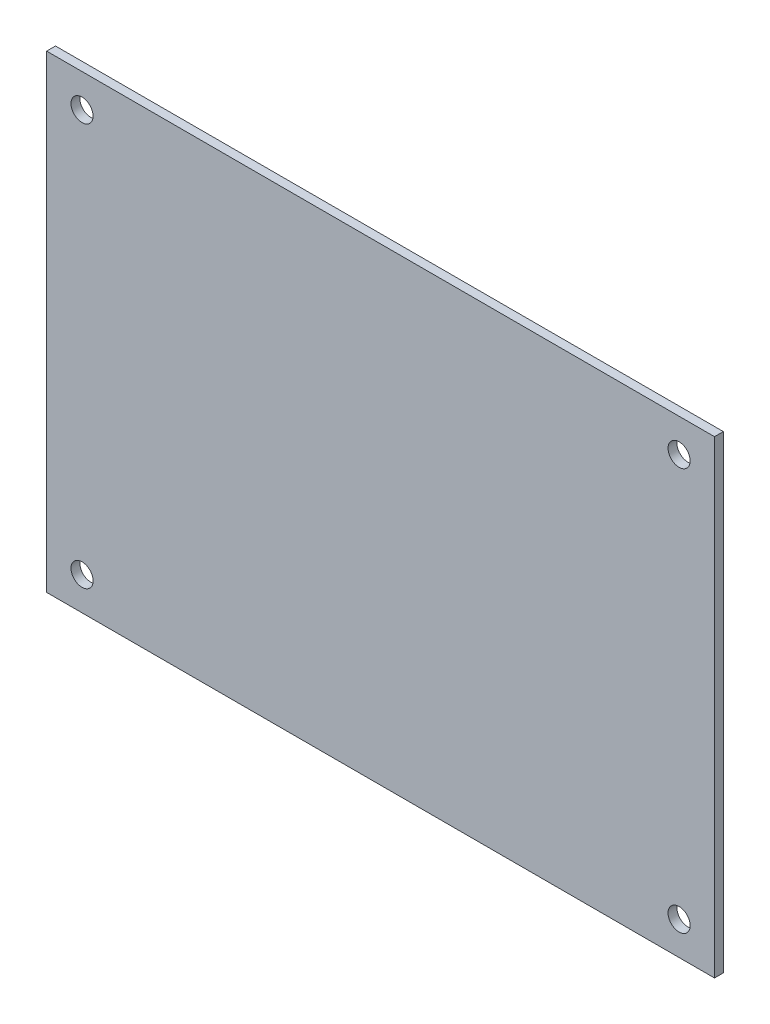
SolidWorks part; units mm, degrees
ref_plane "Front Plane" through (0, 0, 0) normal (0, 0, 1) x (1, 0, 0)
ref_plane "Top Plane" through (0, 0, 0) normal (0, 1, 0) x (1, 0, 0)
ref_plane "Right Plane" through (0, 0, 0) normal (1, 0, 0) x (0, 0, -1)
sketch "Sketch1" plane through (0, 0, 0) normal (0, 0, 1) x (1, 0, 0)
  line L1 (0, 0) -> (155, 0)
  line L2 (0, 0) -> (0, 110)
  line L3 (0, 110) -> (155, 110)
  line L4 (155, 0) -> (155, 110)
  dimension "D1" = 155
  dimension "D2" = 110
extrude "Boss-Extrude1" add sketch "Sketch1" along normal blind 80 contours L2 L1 L4 L3
sketch "Sketch2" plane through (0, 0, 80) normal (0, 0, 1) x (1, 0, 0)
  line L0 (0, 110) -> (2, 110) construction
  line L1 (0, 110) -> (155, 110) construction
  line L2 (0, 110) -> (0, 108) construction
  line L3 (0, 0) -> (0, 110) construction
  line L4 (155, 0) -> (155, 2) construction
  line L5 (155, 0) -> (155, 110) construction
  line L6 (155, 0) -> (153, 0) construction
  line L7 (0, 0) -> (155, 0) construction
  line L8 (0, 108) -> (2, 108) construction
  line L9 (2, 108) -> (2, 110) construction
  line L10 (155, 2) -> (153, 2) construction
  line L11 (153, 2) -> (153, 0) construction
  line L13 (153, 2) -> (2, 2)
  line L14 (153, 2) -> (153, 108)
  line L15 (153, 108) -> (2, 108)
  line L16 (2, 2) -> (2, 108)
  dimension "D1" = 2
  dimension "D2" = 2
  dimension "D3" = 2
  dimension "D4" = 2
extrude "Cut-Extrude1" cut sketch "Sketch2" against normal blind 78 contours L14 L13 L16 L15
sketch "Sketch3" plane through (0, 0, 2) normal (0, 0, 1) x (1, 0, 0)
  line L0 (2, 2) -> (6, 2) construction
  line L1 (153, 2) -> (2, 2) construction
  line L2 (153, 2) -> (149, 2) construction
  line L3 (2, 108) -> (6, 108) construction
  line L4 (153, 108) -> (2, 108) construction
  line L5 (2, 108) -> (2, 104.5) construction
  line L6 (2, 2) -> (2, 108) construction
  line L7 (149, 2) -> (149, 5.5) construction
  line L8 (2, 104.5) -> (6, 104.5) construction
  line L9 (6, 104.5) -> (6, 108) construction
  line L10 (6, 5.5) -> (10, 5.5) construction
  line L11 (6, 104.5) -> (149, 104.5)
  line L12 (6, 104.5) -> (6, 5.5)
  line L13 (6, 5.5) -> (149, 5.5)
  line L14 (149, 104.5) -> (149, 5.5)
  line L15 (10, 5.5) -> (10, 9.5) construction
  line L16 (149, 104.5) -> (145, 104.5) construction
  line L17 (145, 104.5) -> (145, 100.5) construction
  line L19 (10, 9.5) -> (145, 9.5)
  line L20 (10, 9.5) -> (10, 100.5)
  line L21 (10, 100.5) -> (145, 100.5)
  line L22 (145, 9.5) -> (145, 100.5)
  circle A0 centre (145, 100.5) radius 2.5
  circle A1 centre (145, 9.5) radius 2.5
  circle A2 centre (10, 9.5) radius 2.5
  circle A3 centre (10, 100.5) radius 2.5
  dimension "D10" = 5
  dimension "D11" = 5
  dimension "D12" = 5
  dimension "D13" = 5
  dimension "D1" = 4
  dimension "D2" = 3.5
  dimension "D3" = 4
  dimension "D4" = 4
  dimension "D5" = 3.5
  dimension "D6" = 4
  dimension "D7" = 4
  dimension "D8" = 4
  dimension "D9" = 4
extrude "Cut-Extrude2" cut sketch "Sketch3" against normal blind 2 contours A3 | A0 | A2 | A1
sketch "Sketch4" plane through (155, 0, 0) normal (1, 0, 0) x (0, 0, -1)
  line L1 (-53.75, 59.1) -> (-26.25, 59.1)
  line L3 (0, 55) -> (-80, 55) construction
  line L4 (0, 0) -> (0, 110) construction
  line L5 (-80, 0) -> (-80, 110) construction
  line L7 (-26.25, 105.9) -> (-26.25, 59.1)
  line L14 (-53.75, 105.9) -> (-26.25, 105.9)
  line L15 (-53.75, 105.9) -> (-53.75, 59.1)
  dimension "D1" = 46.8
  dimension "D2" = 27.5
sketch "Sketch7" plane through (0, 110, 0) normal (0, 1, 0) x (1, 0, 0)
  line L0 (0, -40) -> (155, -40) construction
  line L1 (0, -80) -> (0, 0) construction
  line L2 (155, -80) -> (155, 0) construction
  line L3 (77.5, 0) -> (77.5, -80) construction
  line L4 (0, 0) -> (155, 0) construction
  line L5 (0, -80) -> (155, -80) construction
  line L6 (110.52, -65.4) -> (95.28, -65.4) construction
  line L7 (44.48, -65.4) -> (110.52, -65.4)
  line L8 (44.48, -65.4) -> (44.48, -14.6)
  line L9 (44.48, -14.6) -> (110.52, -14.6)
  line L10 (110.52, -65.4) -> (110.52, -14.6)
  line L11 (44.48, -65.4) -> (110.52, -14.6) construction
  line L12 (44.48, -14.6) -> (110.52, -65.4) construction
  line L13 (95.28, -65.4) -> (95.28, -62.86) construction
  line L14 (110.52, -14.6) -> (95.28, -14.6) construction
  line L15 (44.48, -14.6) -> (44.48, -20.1445) construction
  line L16 (44.48, -65.4) -> (44.48, -47.62) construction
  line L17 (95.28, -14.6) -> (95.28, -17.14) construction
  line L18 (44.48, -65.4) -> (44.48, -19.68) construction
  circle A0 centre (44.48, -20.1445) radius 1.6
  circle A1 centre (95.28, -17.14) radius 1.6
  circle A2 centre (95.28, -62.86) radius 1.6
  circle A3 centre (44.48, -47.62) radius 1.6
  point P12 (77.5, -40)
  dimension "D9" = 3.2
  dimension "D10" = 3.2
  dimension "D11" = 3.2
  dimension "D12" = 3.2
  dimension "D1" = 66.04
  dimension "D2" = 50.8
  dimension "D3" = 15.24
  dimension "D4" = 2.54
  dimension "D5" = 15.24
  dimension "D6" = 2.54
  dimension "D7" = 17.78
  dimension "D8" = 45.72
extrude "Cut-Extrude7" cut sketch "Sketch7" against normal blind 2 contours A0 | A1 | A3 | A2
extrude "Cut-Extrude8" cut sketch "Sketch4" against normal blind 2
sketch "Sketch8" plane through (155, 0, 0) normal (1, 0, 0) x (0, 0, -1)
  line L0 (-80, 55) -> (0, 55) construction
  line L1 (-80, 0) -> (-80, 110) construction
  line L2 (0, 0) -> (0, 110) construction
  line L3 (0, 0) -> (-2, 0) construction
  line L4 (-80, 0) -> (0, 0) construction
  line L5 (-2, 0) -> (-2, 2) construction
  line L6 (-80, 0) -> (-78, 0) construction
  line L7 (-78, 0) -> (-78, 2) construction
  line L8 (-70, 2) -> (-70, 55)
  line L9 (-78, 2) -> (-74, 2)
  line L10 (-78, 2) -> (-78, 55)
  line L11 (-78, 55) -> (-74, 55)
  line L12 (-74, 2) -> (-74, 55)
  line L13 (-70, 2) -> (-66, 2)
  line L14 (-66, 2) -> (-66, 55)
  line L15 (-70, 55) -> (-66, 55)
  line L16 (-62, 2) -> (-62, 55)
  line L17 (-62, 2) -> (-58, 2)
  line L18 (-58, 2) -> (-58, 55)
  line L19 (-62, 55) -> (-58, 55)
  line L20 (-54, 2) -> (-54, 55)
  line L21 (-54, 2) -> (-50, 2)
  line L22 (-50, 2) -> (-50, 55)
  line L23 (-54, 55) -> (-50, 55)
  line L24 (-46, 2) -> (-46, 55)
  line L25 (-46, 2) -> (-42, 2)
  line L26 (-42, 2) -> (-42, 55)
  line L27 (-46, 55) -> (-42, 55)
  line L28 (-38, 2) -> (-38, 55)
  line L29 (-38, 2) -> (-34, 2)
  line L30 (-34, 2) -> (-34, 55)
  line L31 (-38, 55) -> (-34, 55)
  line L32 (-30, 2) -> (-30, 55)
  line L33 (-30, 2) -> (-26, 2)
  line L34 (-26, 2) -> (-26, 55)
  line L35 (-30, 55) -> (-26, 55)
  line L36 (-22, 2) -> (-22, 55)
  line L37 (-22, 2) -> (-18, 2)
  line L38 (-18, 2) -> (-18, 55)
  line L39 (-22, 55) -> (-18, 55)
  line L40 (-14, 2) -> (-14, 55)
  line L41 (-14, 2) -> (-10, 2)
  line L42 (-10, 2) -> (-10, 55)
  line L43 (-14, 55) -> (-10, 55)
  line L44 (-6, 2) -> (-6, 55)
  line L45 (-6, 2) -> (-2, 2)
  line L46 (-2, 2) -> (-2, 55)
  line L47 (-6, 55) -> (-2, 55)
  dimension "D1" = 2
  dimension "D2" = 2
  dimension "D3" = 2
  dimension "D4" = 2
  dimension "D5" = 4
extrude "Cut-Extrude9" cut sketch "Sketch8" against normal blind 2
sketch "Sketch9" plane through (0, 110, 0) normal (0, 1, 0) x (1, 0, 0)
  line L0 (0, -40) -> (155, -40) construction
  line L1 (0, -80) -> (0, 0) construction
  line L2 (155, -80) -> (155, 0) construction
  line L3 (155, -40) -> (120, -40) construction
  line L4 (120, -40) -> (120, -26) construction
  line L5 (120, -26) -> (113, -26) construction
  line L7 (113, -26) -> (127, -26)
  line L8 (113, -26) -> (113, -12)
  line L9 (113, -12) -> (127, -12)
  line L10 (127, -26) -> (127, -12)
  dimension "D1" = 35
  dimension "D2" = 14
  dimension "D3" = 7
  dimension "D4" = 14
  dimension "D5" = 14
extrude "Cut-Extrude10" cut sketch "Sketch9" against normal blind 2
sketch "Sketch10" plane through (0, 0, 0) normal (-1, 0, 0) x (0, 0, 1)
  line L0 (40, 110) -> (40, 0) construction
  line L1 (80, 110) -> (0, 110) construction
  line L2 (80, 0) -> (0, 0) construction
  line L3 (80, 55) -> (0, 55) construction
  line L4 (80, 0) -> (80, 110) construction
  line L5 (0, 0) -> (0, 110) construction
  line L6 (40, 55) -> (80, 55) construction
  line L7 (80, 55) -> (60, 55) construction
  line L8 (60, 55) -> (58, 55) construction
  line L9 (40, 95) -> (42.5, 95) construction
  line L10 (40, 15) -> (76, 15)
  line L11 (40, 15) -> (40, 95)
  line L12 (40, 95) -> (76, 95)
  line L13 (76, 15) -> (76, 95)
  line L14 (40, 15) -> (76, 95) construction
  line L15 (40, 95) -> (76, 15) construction
  line L16 (42.5, 95) -> (42.5, 92.5) construction
  line L17 (76, 15) -> (73.5, 15) construction
  line L18 (73.5, 15) -> (73.5, 17.5) construction
  line L19 (76, 15) -> (76, 19.4) construction
  line L20 (42.5, 92.5) -> (73.5, 92.5)
  line L21 (42.5, 92.5) -> (42.5, 17.5)
  line L22 (42.5, 17.5) -> (73.5, 17.5)
  line L23 (73.5, 92.5) -> (73.5, 17.5)
  line L24 (76, 19.4) -> (70.6, 19.4) construction
  line L25 (40, 95) -> (45.4, 95) construction
  line L26 (45.4, 95) -> (45.4, 90.6) construction
  line L28 (45.4, 90.6) -> (70.6, 90.6)
  line L29 (45.4, 90.6) -> (45.4, 19.4)
  line L30 (45.4, 19.4) -> (70.6, 19.4)
  line L31 (70.6, 90.6) -> (70.6, 19.4)
  circle A0 centre (73.5, 92.5) radius 1.25
  circle A1 centre (73.5, 17.5) radius 1.25
  circle A2 centre (42.5, 17.5) radius 1.25
  circle A3 centre (42.5, 92.5) radius 1.25
  dimension "D8" = 2.5
  dimension "D9" = 2.5
  dimension "D10" = 2.5
  dimension "D11" = 2.5
  dimension "D1" = 2
  dimension "D2" = 80
  dimension "D3" = 36
  dimension "D4" = 2.5
  dimension "D5" = 2.5
  dimension "D6" = 2.5
  dimension "D7" = 2.5
  dimension "D12" = 4.4
  dimension "D13" = 5.4
  dimension "D14" = 4.4
  dimension "D15" = 5.4
extrude "Cut-Extrude12" cut sketch "Sketch10" against normal blind 2 contours L31 L28 L29 L30 | A3 | A0 | A2 | A1
sketch "Sketch11" plane through (0, 0, 0) normal (-1, 0, 0) x (0, 0, 1)
  line L0 (40, 110) -> (40, 0) construction
  line L1 (80, 110) -> (0, 110) construction
  line L2 (80, 0) -> (0, 0) construction
  line L3 (20, 110) -> (20, 0) construction
  line L4 (0, 55) -> (0, 110) construction
  line L5 (0, 0) -> (0, 110) construction
  line L6 (40, 55) -> (0, 55) construction
  line L7 (0, 82.5) -> (40, 82.5) construction
  circle A0 centre (20, 55) radius 2.5
  circle A1 centre (20, 40) radius 2.5
  circle A2 centre (20, 25) radius 2.5
  circle A3 centre (20, 82.5) radius 4.5
  dimension "D1" = 5
  dimension "D3" = 9
  dimension "D2" = 3
extrude "Cut-Extrude13" cut sketch "Sketch11" against normal blind 2
sketch "Sketch12" plane through (0, 0, 80) normal (0, 0, 1) x (1, 0, 0)
  line L0 (2, 108) -> (0, 108) construction
  line L1 (0, 0) -> (0, 110) construction
  line L2 (153, 108) -> (155, 108) construction
  line L3 (155, 0) -> (155, 110) construction
  line L4 (2, 2) -> (2, 0) construction
  line L5 (0, 0) -> (155, 0) construction
  line L6 (153, 2) -> (153, 0) construction
  line L8 (0, 108) -> (2, 108)
  line L9 (0, 108) -> (0, 0)
  line L10 (0, 0) -> (2, 0)
  line L11 (2, 108) -> (2, 0)
  line L12 (153, 108) -> (155, 108)
  line L13 (153, 108) -> (153, 0)
  line L14 (153, 0) -> (155, 0)
  line L15 (155, 108) -> (155, 0)
  line L16 (2, 0) -> (153, 0)
  line L17 (2, 0) -> (2, 2)
  line L18 (2, 2) -> (153, 2)
  line L19 (153, 0) -> (153, 2)
  line L20 (155, 108) -> (0, 108)
  line L21 (155, 108) -> (155, 110)
  line L22 (155, 110) -> (0, 110)
  line L23 (0, 108) -> (0, 110)
  line M1 (2, 108) -> (153, 108)
  line M2 (153, 108) -> (153, 2)
  line M3 (153, 2) -> (2, 2)
  line M4 (2, 2) -> (2, 108)
  line M5 (155, 110) -> (0, 110)
  line M6 (0, 110) -> (0, 0)
  line M7 (0, 0) -> (155, 0)
  line M8 (155, 0) -> (155, 110)
extrude "Cut-Extrude14" cut sketch "Sketch12" against normal blind 80 contours L12 L8 M1 M8 M5 M6 | L11 L8 M4 M6 M7 | L13 L12 M2 M7 M8 | L13 L11 M3 M7
